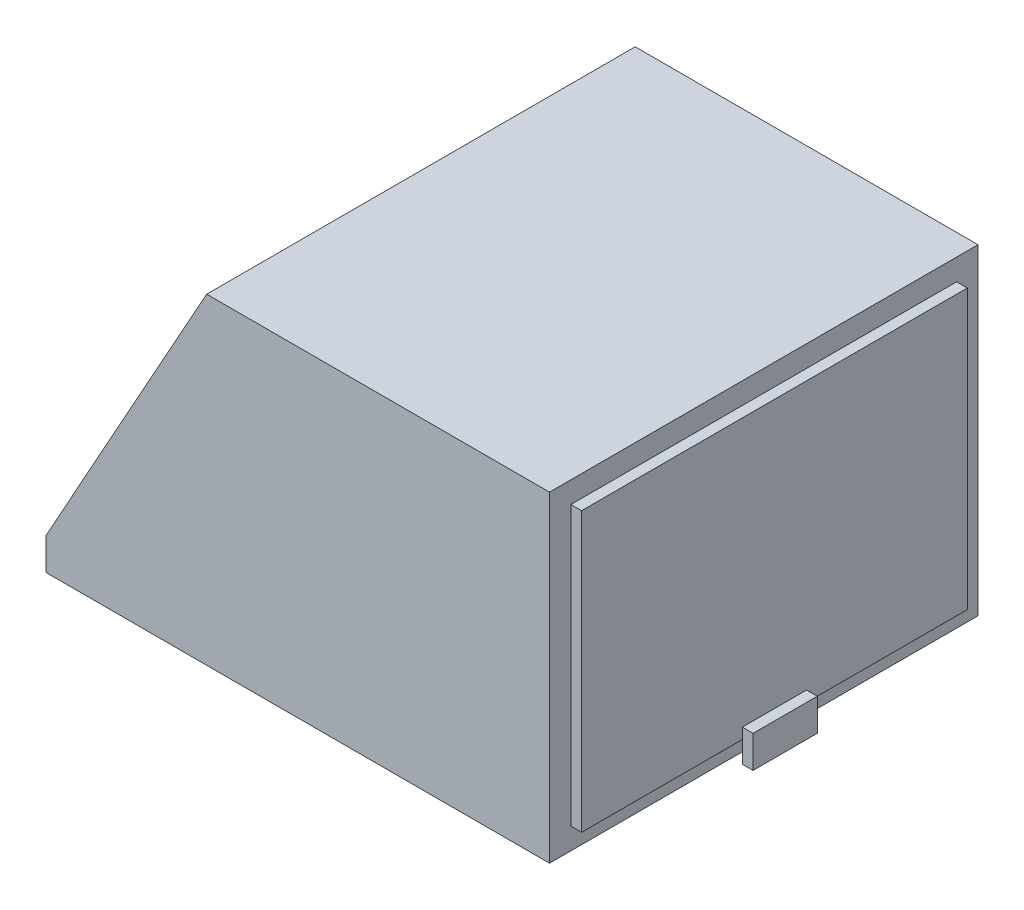
SolidWorks part; units mm, degrees
ref_plane "Front Plane" through (0, 0, 0) normal (0, 0, 1) x (1, 0, 0)
ref_plane "Top Plane" through (0, 0, 0) normal (0, 1, 0) x (1, 0, 0)
ref_plane "Right Plane" through (0, 0, 0) normal (1, 0, 0) x (0, 0, -1)
sketch "Sketch1" plane through (0, 0, 0) normal (0, 0, 1) x (1, 0, 0)
  line L1 (-34.7458, 15.5932) -> (15.2542, 15.5932)
  line L2 (-34.7458, 15.5932) -> (-34.7458, -14.4068)
  line L3 (-34.7458, -14.4068) -> (15.2542, -14.4068)
  line L4 (15.2542, 15.5932) -> (15.2542, -14.4068)
  dimension "D1" = 30
  dimension "D2" = 50
extrude "Boss-Extrude1" add sketch "Sketch1" along normal blind 40
sketch "Sketch29" plane through (0, 0, 40) normal (0, 0, 1) x (1, 0, 0)
  line L0 (-34.7458, -11.4068) -> (-19.7458, 15.5932)
  line L1 (-34.7458, 15.5932) -> (-34.7458, -14.4068) construction
  line L2 (15.2542, 15.5932) -> (-34.7458, 15.5932) construction
  line L3 (-19.7458, 15.5932) -> (-34.7458, 15.5932)
  line L4 (-34.7458, 15.5932) -> (-34.7458, -11.4068)
  dimension "D1" = 15
  dimension "D2" = 27
extrude "Cut-Extrude15" cut sketch "Sketch29" against normal blind 40
sketch "Sketch33" plane through (-21.7085, 12.0603, 0) normal (-0.8742, 0.4856, 0) x (0, 0, 1)
  line L0 (0, -26.8454) -> (0, 4.0415) construction
  line L1 (1, 2.5415) -> (39, 2.5415)
  line L2 (1, 2.5415) -> (1, -25.3454)
  line L3 (1, -25.3454) -> (39, -25.3454)
  line L4 (39, 2.5415) -> (39, -25.3454)
  line L5 (40, -26.8454) -> (40, 4.0415) construction
  line L6 (0, -26.8454) -> (40, -26.8454) construction
  line L7 (0, 4.0415) -> (40, 4.0415) construction
  dimension "D1" = 1
  dimension "D2" = 1
  dimension "D3" = 1.5
  dimension "D4" = 1.5
extrude "Cut-Extrude16" cut sketch "Sketch33" against normal blind 1
sketch "Sketch36" plane through (0, 0, 40) normal (0, 0, 1) x (1, 0, 0)
  line L0 (-34.7458, -14.4068) -> (15.2542, -14.4068) construction
  line L1 (15.2542, 15.5932) -> (12.2542, 15.5932)
  line L2 (15.2542, 15.5932) -> (15.2542, -14.4068)
  line L3 (15.2542, -14.4068) -> (12.2542, -14.4068)
  line L4 (12.2542, 15.5932) -> (12.2542, -14.4068)
  dimension "D1" = 3
extrude "Cut-Extrude17" cut sketch "Sketch36" against normal blind 40
sketch "Sketch37" plane through (12.2542, 0, 0) normal (1, 0, 0) x (0, 0, -1)
  line L0 (-40, 15.5932) -> (-40, -14.4068) construction
  line L1 (-38, 13.5932) -> (-2, 13.5932)
  line L2 (-38, 13.5932) -> (-38, -12.4068)
  line L3 (-38, -12.4068) -> (-2, -12.4068)
  line L4 (-2, 13.5932) -> (-2, -12.4068)
  line L5 (0, 15.5932) -> (0, -14.4068) construction
  line L6 (0, -14.4068) -> (-40, -14.4068) construction
  line L7 (0, 15.5932) -> (-40, 15.5932) construction
  dimension "q" = 2
  dimension "D2" = 2
  dimension "2" = 2
  dimension "D3" = 2
extrude "Boss-Extrude5" add sketch "Sketch37" along normal blind 1
sketch "Sketch38" plane through (13.2542, 0, 0) normal (1, 0, 0) x (0, 0, -1)
  line L0 (0, -14.4068) -> (-40, -14.4068) construction
  line L1 (-23, -11.4068) -> (-17, -11.4068)
  line L2 (-23, -11.4068) -> (-23, -14.4068)
  line L3 (-23, -14.4068) -> (-17, -14.4068)
  line L4 (-17, -11.4068) -> (-17, -14.4068)
  line L5 (-38, 13.5932) -> (-38, -12.4068) construction
  line L6 (-2, -12.4068) -> (-2, 13.5932) construction
  dimension "D1" = 15
  dimension "D2" = 15
  dimension "D3" = 3
extrude "Boss-Extrude6" add sketch "Sketch38" along normal blind 1
